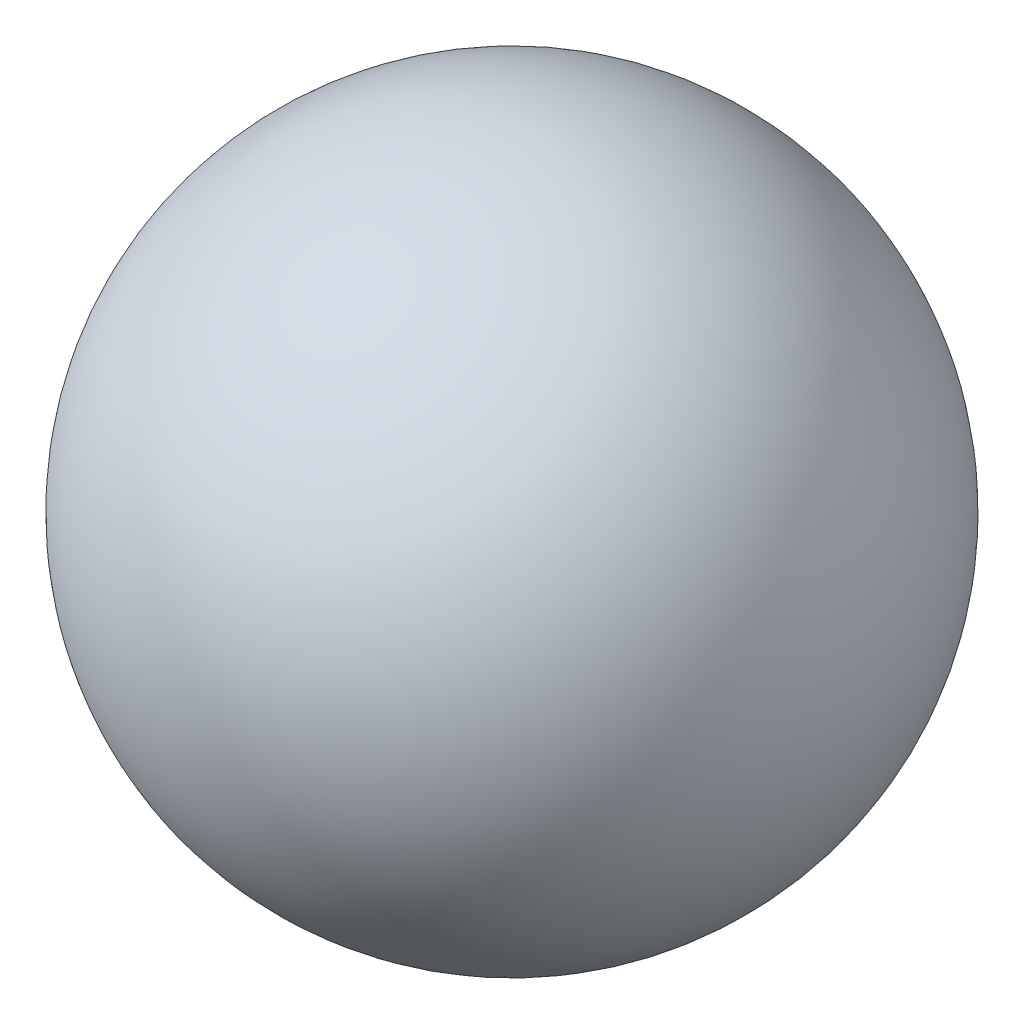
SolidWorks part; units mm, degrees
ref_plane "Front Plane" through (0, 0, 0) normal (0, 0, 1) x (1, 0, 0)
ref_plane "Top Plane" through (0, 0, 0) normal (0, 1, 0) x (1, 0, 0)
ref_plane "Right Plane" through (0, 0, 0) normal (1, 0, 0) x (0, 0, -1)
sketch "Sketch2" plane through (0, 0, 0) normal (0, 1, 0) x (1, 0, 0)
  line L0 (0, 25.4) -> (0, -25.4)
  arc A0 (0, -25.4) -> (0, 25.4) centre (0, 0) ccw
  dimension "D1" = 50.8
revolve "Revolve1" add sketch "Sketch2" angle 360 about L0
